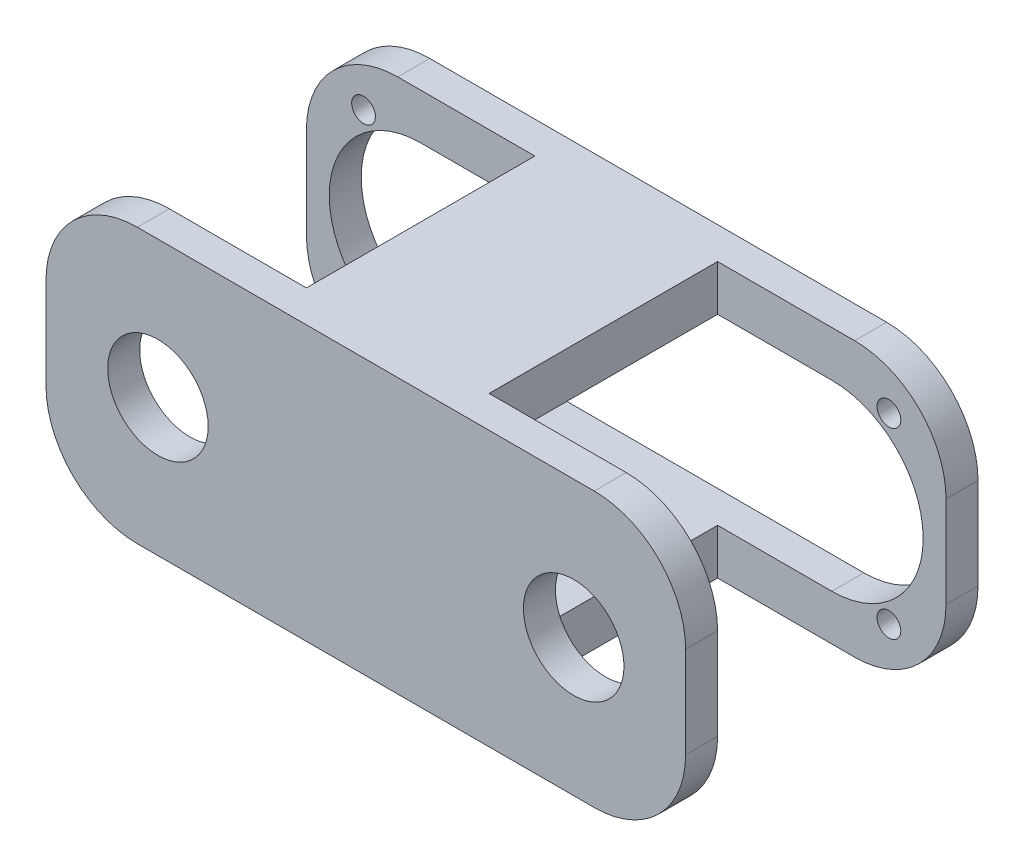
SolidWorks part; units mm, degrees
ref_plane "Front Plane" through (0, 0, 0) normal (0, 0, 1) x (1, 0, 0)
ref_plane "Top Plane" through (0, 0, 0) normal (0, 1, 0) x (1, 0, 0)
ref_plane "Right Plane" through (0, 0, 0) normal (1, 0, 0) x (0, 0, -1)
sketch "Sketch2" plane through (0, 0, 0) normal (0, 0, 1) x (1, 0, 0)
  line L1 (-20, 0) -> (-120, 0)
  line L2 (0, 20) -> (0, 40)
  line L3 (-20, 60) -> (-120, 60)
  line L4 (-140, 20) -> (-140, 40)
  line L9 (-115, 50) -> (-25, 50)
  line L11 (-115, 10) -> (-25, 10)
  arc A0 (-120, 0) -> (-140, 20) centre (-120, 20) cw
  arc A1 (-20, 0) -> (0, 20) centre (-20, 20) ccw
  arc A2 (0, 40) -> (-20, 60) centre (-20, 40) ccw
  arc A3 (-120, 60) -> (-140, 40) centre (-120, 40) ccw
  arc A4 (-25, 10) -> (-5, 30) centre (-25, 30) ccw
  arc A5 (-135, 30) -> (-115, 10) centre (-115, 30) ccw
  arc A6 (-25, 50) -> (-5, 30) centre (-25, 30) cw
  arc A7 (-115, 50) -> (-135, 30) centre (-115, 30) ccw
  point P7 (-140, 0)
  point P10 (0, 0)
  point P13 (0, 60)
  dimension "D3" = 20
  dimension "D8" = 20
  dimension "D1" = 60
  dimension "D2" = 140
  dimension "D4" = 10
  dimension "D6" = 10
extrude "Boss-Extrude1" add sketch "Sketch2" along normal blind 7
sketch "Sketch3" plane through (0, 0, 7) normal (0, 0, 1) x (1, 0, 0)
  line L0 (-20, 60) -> (-120, 60) construction
  line L1 (-90, 60) -> (-50, 60)
  line L2 (-90, 60) -> (-90, 50)
  line L3 (-90, 50) -> (-50, 50)
  line L4 (-50, 60) -> (-50, 50)
  line L6 (-140, 40) -> (-140, 20) construction
  line L8 (-140, 30) -> (0, 30) construction
  line L14 (0, 20) -> (0, 40) construction
  line L15 (-90, 10) -> (-50, 10)
  line L16 (-50, 0) -> (-50, 10)
  line L17 (-90, 0) -> (-50, 0)
  line L18 (-90, 0) -> (-90, 10)
  dimension "D1" = 10
  dimension "D2" = 40
  dimension "4" = 50
extrude "Boss-Extrude2" add sketch "Sketch3" along normal blind 50
sketch "Sketch4" plane through (0, 0, 57) normal (0, 0, 1) x (1, 0, 0)
  line L0 (-70, 60) -> (-70, 0) construction
  line L1 (-120, 60) -> (-20, 60)
  line L2 (-140, 40) -> (-140, 20)
  line L3 (-120, 0) -> (-20, 0)
  line L4 (0, 40) -> (0, 20)
  arc A0 (-140, 20) -> (-120, 0) centre (-120, 20) ccw
  arc A1 (-20, 0) -> (0, 20) centre (-20, 20) ccw
  arc A2 (-20, 60) -> (0, 40) centre (-20, 40) cw
  arc A3 (-120, 60) -> (-140, 40) centre (-120, 40) ccw
  circle A4 centre (-115.5, 30) radius 11
  circle A5 centre (-24.5, 30) radius 11
  point P7 (-140, 0)
  point P10 (0, 0)
  point P13 (0, 60)
  point P16 (-140, 60)
  dimension "D3" = 20
  dimension "D6" = 22
  dimension "D1" = 60
  dimension "D2" = 140
  dimension "D4" = 30
  dimension "D5" = 24.5
extrude "Boss-Extrude3" add sketch "Sketch4" along normal blind 7
sketch "Sketch6" plane through (0, 0, 0) normal (0, 0, -1) x (-1, 0, 0)
  line L0 (20, 60) -> (120, 60) construction
  line L1 (0, 20) -> (0, 40) construction
  line L2 (70, 60) -> (70, 0) construction
  line L3 (120, 0) -> (20, 0) construction
  line L4 (0, 30) -> (140, 30) construction
  line L5 (140, 40) -> (140, 20) construction
  circle A0 centre (12.5, 50) radius 2.6
  circle A1 centre (127.5, 50) radius 2.6
  circle A2 centre (127.5, 10) radius 2.6
  circle A3 centre (12.5, 10) radius 2.6
  dimension "D1" = 5.2
  dimension "D2" = 10
  dimension "D3" = 12.5
extrude "Cut-Extrude1" cut sketch "Sketch6" against normal blind 7
